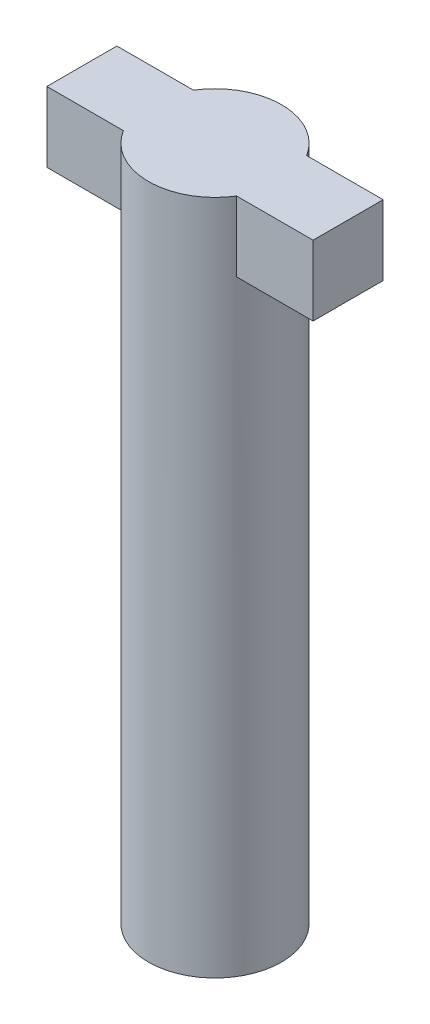
SolidWorks part; units mm, degrees
ref_plane "Front Plane" through (0, 0, 0) normal (0, 0, 1) x (1, 0, 0)
ref_plane "Top Plane" through (0, 0, 0) normal (0, 1, 0) x (1, 0, 0)
ref_plane "Right Plane" through (0, 0, 0) normal (1, 0, 0) x (0, 0, -1)
sketch "Sketch1" plane through (0, 0, 0) normal (0, 1, 0) x (1, 0, 0)
  circle A0 centre (0, 0) radius 0.95
  dimension "D1" = 1.9
extrude "Body" add sketch "Sketch1" along normal blind 9.65
sketch "Sketch2" plane through (0, 9.65, 0) normal (0, 1, 0) x (1, 0, 0)
  line L0 (0, 0) -> (-1.9, 0) construction
  line L1 (0, 0.5) -> (-1.9, 0.5)
  line L2 (0, -0.5) -> (-1.9, -0.5)
  line L3 (-1.9, 0.5) -> (-1.9, -0.5)
  line L4 (0, 0) -> (0, 0.2952) construction
  line L5 (0, 0) -> (1.9, 0) construction
  line L6 (0, -0.5) -> (1.9, -0.5)
  line L7 (1.9, 0.5) -> (1.9, -0.5)
  line L8 (0, 0.5) -> (1.9, 0.5)
  circle A0 centre (0, 0) radius 0.95 construction
  circle A1 centre (0, 0) radius 0.95
  circle M6 centre (0, 0) radius 0.95
  dimension "D1" = 1.9
  dimension "D2" = 0.5
  dimension "D3" = 0.5
extrude "Lock" add sketch "Sketch2" against normal blind 1 contours L1 L3 L2 M6 | L8 L6 L7 M6
equation "\"BoltD\"=2mm"
equation "\"NutShortSide\"=4mm"
equation "\"NutLongSide\"=4.5mm"
equation "\"SmallScrewD\"=1.2mm"
equation "\"SmallScrewHatD\"=2mm"
equation "\"TubeOuterD\"=1.2mm"
equation "\"BasicPulleyD\"=15mm"
equation "\"GrooveDepth\"=0.7mm"
equation "\"Cable1D\"=0.4mm"
equation "\"Cable2D\"=0.3mm"
equation "\"BallBearingInnerD\"=2mm"
equation "\"BallBearingOuterD\"=4mm"
equation "\"D1@Sketch1\"=\"BallBearingInnerD\"-0.1"
equation "\"BoltHatD\"=3.2mm"
equation "\"BallBearingThickness\"=2mm"
equation "\"BearingCapD\"=12mm"
equation "\"HumerusL\"=37.2mm"
equation "\"HumerusElbowSidePulleyD\"=10mm"
equation "\"RadiusL\"=68.1mm"
equation "\"Finger1L\"=120mm"
equation "\"Finger2L\"=100mm"
equation "\"Finger3L\"=80mm"
equation "\"ElbowExtendedAngle\"=140deg"
equation "\"ElbowFlexedAngle\"=38deg"
equation "\"TubeClipW\"=1.5mm"
equation "\"TubeClipH\"=1mm"
equation "\"TubeClipLock_SideL\"=1.6mm"
equation "\"TubeClipLock_W\"=0.7mm"
equation "\"Digit5ExtendedAngle\"=80deg"
equation "\"Digit5FlexedAngle\"=24deg"
equation "\"Digit4ExtendedAngle\"=108deg"
equation "\"Digit4FlexedAngle\"=34deg"
equation "\"Digit3ExtendedAngle\"=145deg"
equation "\"Digit3FlexedAngle\"=44deg"
